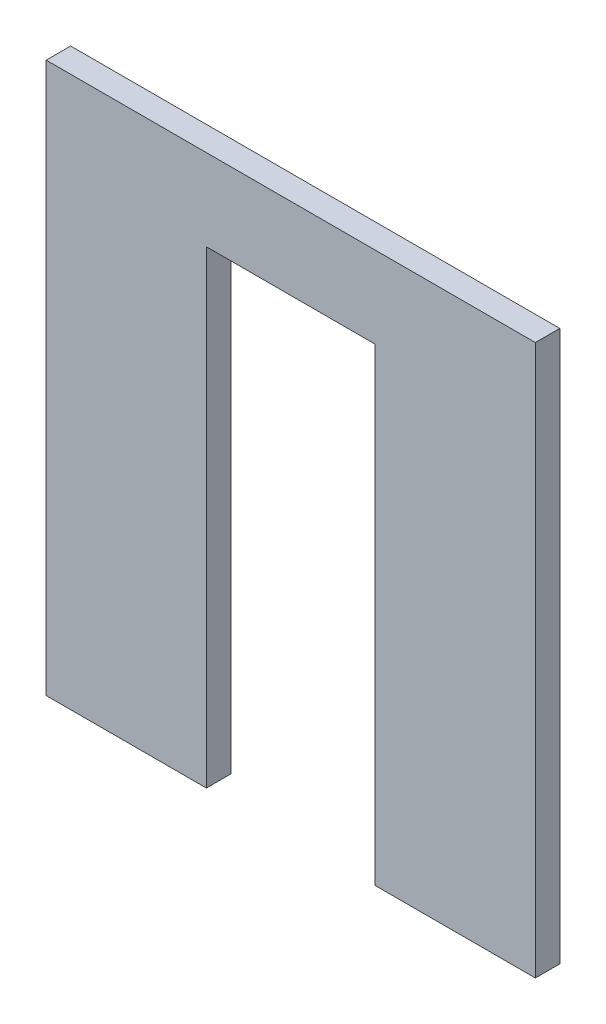
SolidWorks part; units mm, degrees
ref_plane "Front Plane" through (0, 0, 0) normal (0, 0, 1) x (1, 0, 0)
ref_plane "Top Plane" through (0, 0, 0) normal (0, 1, 0) x (1, 0, 0)
ref_plane "Right Plane" through (0, 0, 0) normal (1, 0, 0) x (0, 0, -1)
sketch "Sketch1" plane through (0, 0, 0) normal (0, 0, 1) x (1, 0, 0)
  line L1 (0, 0) -> (0.0197, 0)
  line L2 (0, 0) -> (0, 0.055)
  line L4 (0.0197, 0) -> (0.0197, 0.0575)
  line L5 (0.0197, 0.0575) -> (0.0403, 0.0575)
  line L6 (0, 0.055) -> (0, 0.0675)
  line L7 (0, 0.0675) -> (0.06, 0.0675)
  line L8 (0.06, 0.055) -> (0.06, 0.0675)
  line L10 (0.06, 0.055) -> (0.06, 0)
  line L11 (0.06, 0) -> (0.0404, 0)
  line L12 (0.0403, 0.0575) -> (0.0404, 0)
  dimension "D1" = 0.06
  dimension "D2" = 0.0125
  dimension "D3" = 0.0197
  dimension "D4" = 0.0197
  dimension "D5" = 0.055
  dimension "D6" = 0.055
extrude "Boss-Extrude1" add sketch "Sketch1" along normal blind 0.003
